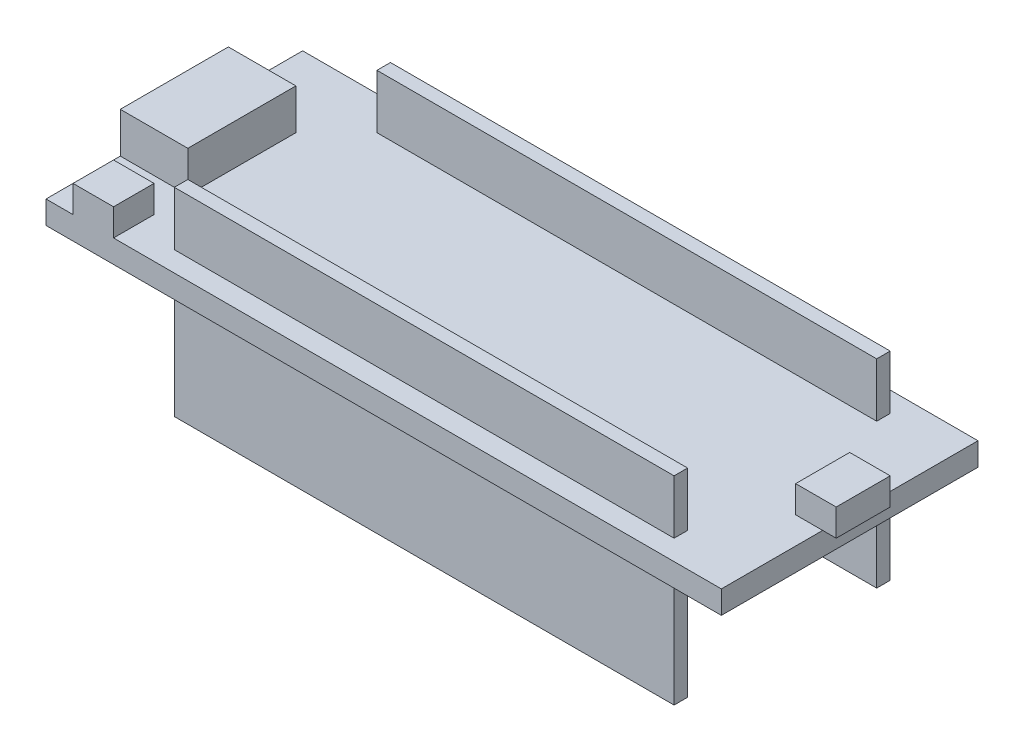
SolidWorks part; units mm, degrees
ref_plane "Спереди" through (0, 0, 0) normal (0, 0, 1) x (1, 0, 0)
ref_plane "Сверху" through (0, 0, 0) normal (0, 1, 0) x (1, 0, 0)
ref_plane "Справа" through (0, 0, 0) normal (1, 0, 0) x (0, 0, -1)
other "Центр тяжести"
sketch "Эскиз1" plane through (0, 0, 0) normal (0, 1, 0) x (1, 0, 0)
  line L1 (-25, -9.5) -> (25, -9.5)
  line L2 (-25, -9.5) -> (-25, 9.5)
  line L3 (-25, 9.5) -> (25, 9.5)
  line L4 (25, -9.5) -> (25, 9.5)
  line L5 (-25, -9.5) -> (25, 9.5) construction
  line L6 (-25, 9.5) -> (25, -9.5) construction
  point P0 (0, 0)
  dimension "D1" = 50
  dimension "D2" = 19
extrude "Бобышка-Вытянуть1" add sketch "Эскиз1" along normal blind 1.7
sketch "Эскиз2" plane through (0, 1.7, 0) normal (0, 1, 0) x (1, 0, 0)
  line L0 (-25, 9.5) -> (-25, -9.5) construction
  line L1 (-20, 4) -> (-25, 4)
  line L2 (-20, 4) -> (-20, -4)
  line L3 (-20, -4) -> (-25, -4)
  line L4 (-25, 4) -> (-25, -4)
  line L5 (-20, 4) -> (-25, -4) construction
  line L6 (-20, -4) -> (-25, 4) construction
  line L7 (33.4258, 0) -> (-35.8999, 0) construction
  point P0 (-22.5, 0)
  dimension "D1" = 5
  dimension "D2" = 8
extrude "Бобышка-Вытянуть2" add sketch "Эскиз2" along normal blind 3
sketch "Эскиз3" plane through (0, 1.7, 0) normal (0, 1, 0) x (1, 0, 0)
  line L0 (-25, -9.5) -> (25, -9.5) construction
  line L1 (-20, -9.5) -> (-23, -9.5)
  line L2 (-20, -9.5) -> (-20, -6.5)
  line L3 (-20, -6.5) -> (-23, -6.5)
  line L4 (-23, -9.5) -> (-23, -6.5)
  line L5 (-25, -4) -> (-25, -9.5) construction
  dimension "D1" = 2
  dimension "D2" = 3
  dimension "D3" = 3
extrude "Бобышка-Вытянуть3" add sketch "Эскиз3" along normal blind 2
sketch "Эскиз4" plane through (0, 1.7, 0) normal (0, 1, 0) x (1, 0, 0)
  line L6 (31.6187, 0) -> (-38.1006, 0) construction
  line L7 (20, 7) -> (-17, 7)
  line L8 (-17, 8) -> (-17, 7)
  line L9 (20, 8) -> (-17, 8)
  line L10 (20, 8) -> (20, 7)
  line L11 (25, 9.5) -> (-25, 9.5) construction
  line L12 (20, -8) -> (20, -7)
  line L13 (20, -8) -> (-17, -8)
  line L14 (-17, -8) -> (-17, -7)
  line L15 (20, -7) -> (-17, -7)
  dimension "D1" = 1
  dimension "D2" = 1.5
extrude "Бобышка-Вытянуть4" add sketch "Эскиз4" along normal blind 4 and the other way blind 10.7
sketch "Эскиз6" plane through (0, 0, 0) normal (0, -1, 0) x (1, 0, 0)
  line L0 (-25, -9.5) -> (-25, 9.5) construction
  line L1 (-22, -1) -> (-25, -1)
  line L2 (-22, -1) -> (-22, 1)
  line L3 (-22, 1) -> (-25, 1)
  line L4 (-25, -1) -> (-25, 1)
  line L5 (-22, -1) -> (-25, 1) construction
  line L6 (-22, 1) -> (-25, -1) construction
  line L7 (-29.7036, 0) -> (52.9071, 0) construction
  point P0 (-23.5, 0)
  dimension "D1" = 2
  dimension "D2" = 3
extrude "Бобышка-Вытянуть6" add sketch "Эскиз6" along normal blind 1
sketch "Эскиз7" plane through (0, 1.7, 0) normal (0, 1, 0) x (1, 0, 0)
  line L1 (26, -2) -> (23, -2)
  line L2 (26, -2) -> (26, 2)
  line L3 (26, 2) -> (23, 2)
  line L4 (23, -2) -> (23, 2)
  line L6 (23, -2) -> (26, 2) construction
  line L7 (26, -2) -> (23, 2) construction
  line L8 (-5.4773, 0) -> (45.3746, 0) construction
  point P0 (24.5, 0)
  dimension "D1" = 3
  dimension "D2" = 4
extrude "Бобышка-Вытянуть7" add sketch "Эскиз7" along normal blind 2
